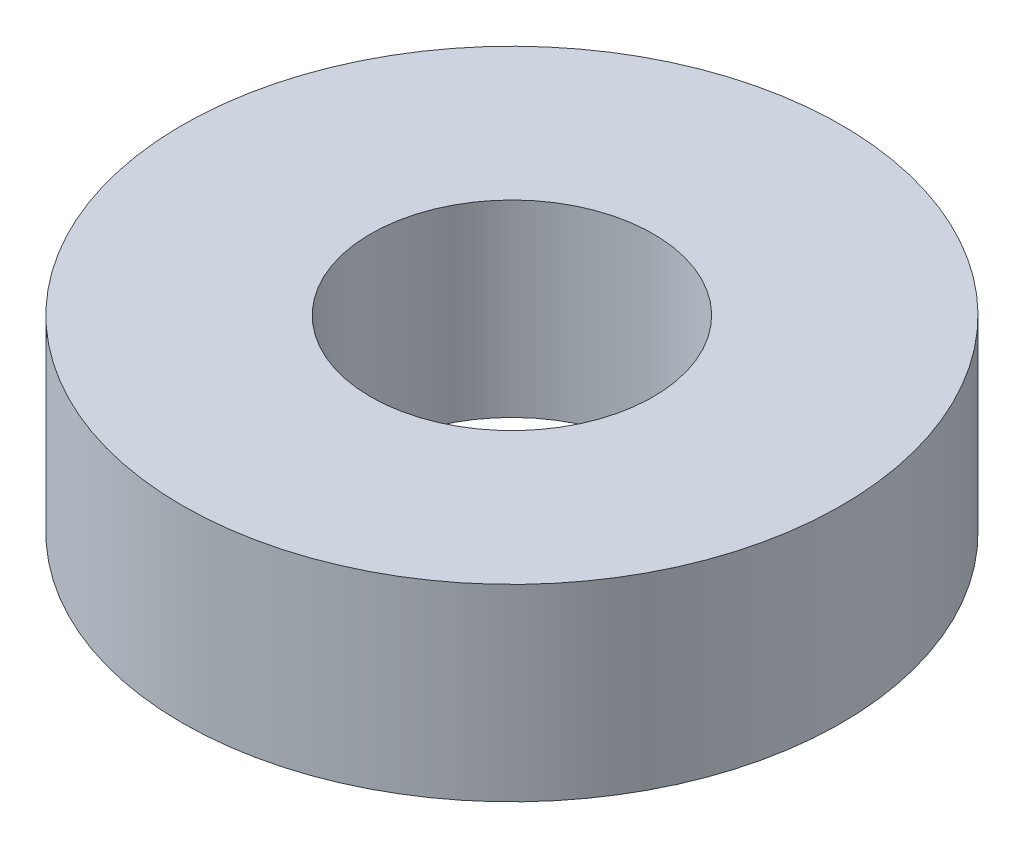
SolidWorks part; units mm, degrees
ref_plane "Plan de face" through (0, 0, 0) normal (0, 0, 1) x (1, 0, 0)
ref_plane "Plan de dessus" through (0, 0, 0) normal (0, 1, 0) x (1, 0, 0)
ref_plane "Plan de droite" through (0, 0, 0) normal (1, 0, 0) x (0, 0, -1)
sketch "Esquisse1" plane through (0, 0, 0) normal (0, 1, 0) x (1, 0, 0)
  circle A0 centre (0, 0) radius 6
  circle A1 centre (0, 0) radius 14
  dimension "D1" = 12
  dimension "D2" = 28
extrude "Boss.-Extru.1" add sketch "Esquisse1" along normal blind 8
